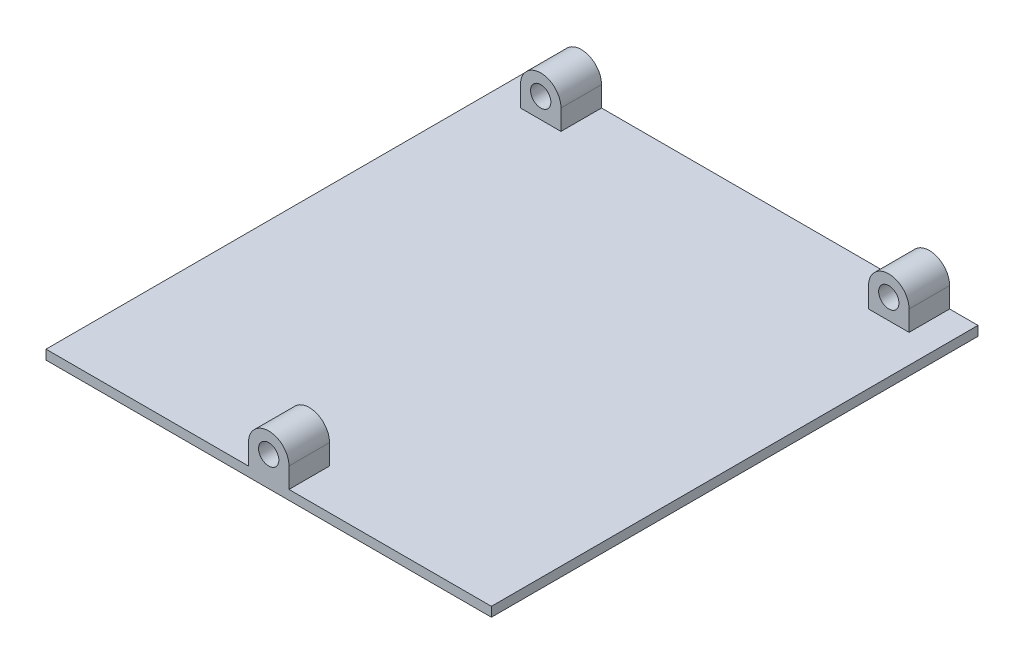
SolidWorks part; units mm, degrees
ref_plane "Front Plane" through (0, 0, 0) normal (0, 0, 1) x (1, 0, 0)
ref_plane "Top Plane" through (0, 0, 0) normal (0, 1, 0) x (1, 0, 0)
ref_plane "Right Plane" through (0, 0, 0) normal (1, 0, 0) x (0, 0, -1)
sketch "Sketch1" plane through (0, 0, 0) normal (0, 1, 0) x (1, 0, 0)
  line L1 (0, 0) -> (139.5, 0)
  line L2 (0, 0) -> (0, 152.4)
  line L3 (0, 152.4) -> (139.5, 152.4)
  line L4 (139.5, 0) -> (139.5, 152.4)
  dimension "D1" = 152.4
  dimension "D2" = 139.5
extrude "Boss-Extrude1" add sketch "Sketch1" along normal blind 6.35
sketch "Sketch2" plane through (0, 6.35, 0) normal (0, 1, 0) x (1, 0, 0)
  line L0 (0, 0) -> (139.5, 0) construction
  line L1 (0, 152.4) -> (139.5, 152.4)
  line L2 (0, 152.4) -> (0, 0)
  line L3 (0, 0) -> (139.5, 0)
  line L4 (139.5, 152.4) -> (139.5, 0)
  line L5 (139.5, 0) -> (139.5, 152.4) construction
extrude "Cut-Extrude1" cut sketch "Sketch2" against normal blind 3.375
sketch "Sketch3" plane through (0, 0, 0) normal (0, 0, 1) x (1, 0, 0)
  line L0 (63.4, 9.325) -> (63.4, 2.975)
  line L1 (63.4, 2.975) -> (76.1, 2.975)
  line L2 (76.1, 9.325) -> (76.1, 2.975)
  line L3 (0, 2.975) -> (139.5, 2.975) construction
  line L4 (139.5, 2.975) -> (0, 2.975) construction
  arc A0 (76.1, 9.325) -> (63.4, 9.325) centre (69.75, 9.325) ccw
  circle A1 centre (69.75, 9.325) radius 3.175
  point P6 (69.75, 2.975)
  point P9 (69.75, 2.975)
  dimension "D1" = 6.35
  dimension "D2" = 12.7
  dimension "D8" = 6.35
  dimension "D5" = 6.35
extrude "Boss-Extrude2" add sketch "Sketch3" against normal blind 12.7
sketch "Sketch4" plane through (0, 0, -152.4) normal (0, 0, -1) x (-1, 0, 0)
  line L0 (-130.61, 9.325) -> (-130.61, 2.975)
  line L1 (-130.61, 2.975) -> (-117.91, 2.975)
  line L2 (-117.91, 9.325) -> (-117.91, 2.975)
  line L3 (-21.59, 9.325) -> (-21.59, 2.975)
  line L4 (-21.59, 2.975) -> (-8.89, 2.975)
  line L5 (-8.89, 9.325) -> (-8.89, 2.975)
  line L6 (-139.5, 2.975) -> (0, 2.975) construction
  line L7 (0, 2.975) -> (0, 0) construction
  line L8 (-139.5, 2.975) -> (-139.5, 0) construction
  arc A0 (-117.91, 9.325) -> (-130.61, 9.325) centre (-124.26, 9.325) ccw
  circle A1 centre (-124.26, 9.325) radius 3.175
  arc A2 (-8.89, 9.325) -> (-21.59, 9.325) centre (-15.24, 9.325) ccw
  circle A3 centre (-15.24, 9.325) radius 3.175
  dimension "D1" = 6.35
  dimension "D3" = 6.35
  dimension "D5" = 6.35
  dimension "D7" = 6.35
  dimension "D2" = 6.35
  dimension "D4" = 12.7
  dimension "D6" = 6.35
  dimension "D8" = 12.7
  dimension "D9" = 8.89
  dimension "D10" = 8.89
  dimension "D11" = 15.24
  dimension "D12" = 15.24
extrude "Boss-Extrude3" add sketch "Sketch4" against normal blind 12.7
